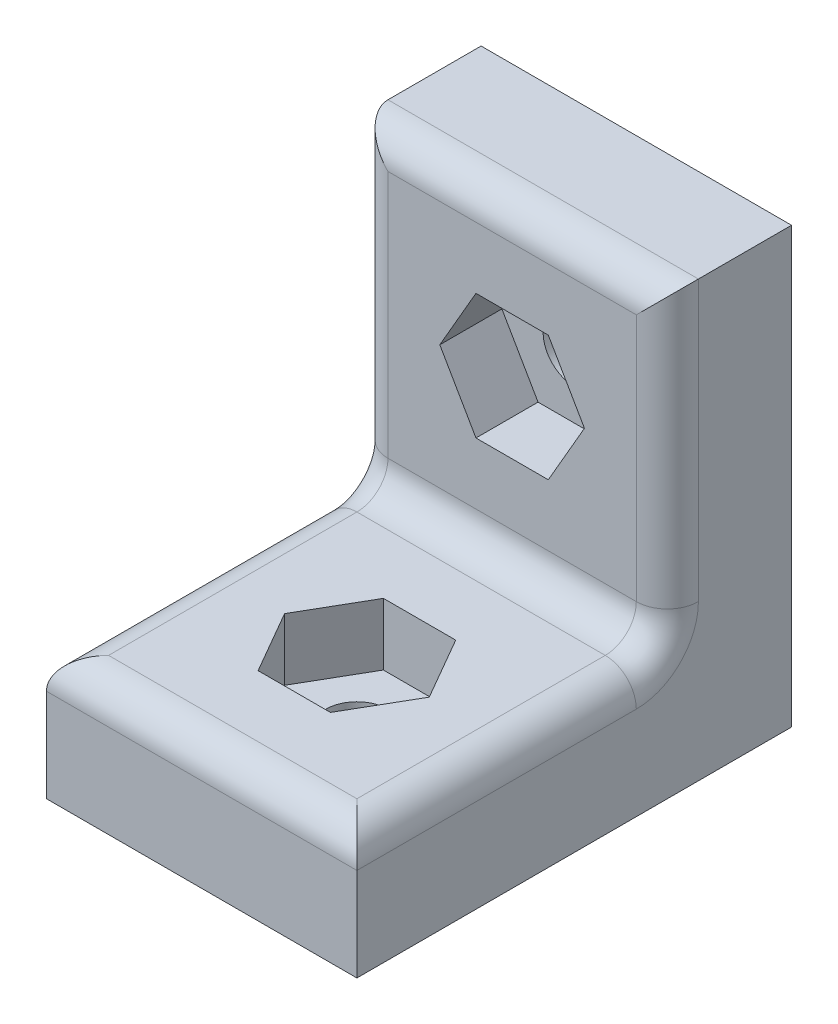
SolidWorks part; units mm, degrees
ref_plane "Plan de face" through (0, 0, 0) normal (0, 0, 1) x (1, 0, 0)
ref_plane "Plan de dessus" through (0, 0, 0) normal (0, 1, 0) x (1, 0, 0)
ref_plane "Plan de droite" through (0, 0, 0) normal (1, 0, 0) x (0, 0, -1)
sketch "Esquisse1" plane through (0, 0, 0) normal (0, 0, 1) x (1, 0, 0)
  line L1 (-5, 14) -> (5, 14)
  line L2 (-5, 14) -> (-5, 0)
  line L3 (-5, 0) -> (5, 0)
  line L4 (5, 14) -> (5, 0)
  dimension "D1" = 10
  dimension "D2" = 14
  dimension "D3" = 5
extrude "Boss.-Extru.1" add sketch "Esquisse1" along normal blind 4
sketch "Esquisse2" plane through (0, 0, 4) normal (0, 0, 1) x (1, 0, 0)
  line L0 (5, 0) -> (5, 14) construction
  line L1 (-5, 0) -> (5, 0)
  line L2 (-5, 0) -> (-5, 4)
  line L3 (-5, 4) -> (5, 4)
  line L4 (5, 0) -> (5, 4)
  dimension "D1" = 4
extrude "Boss.-Extru.2" add sketch "Esquisse2" along normal blind 10
sketch "Esquisse3" plane through (0, 0, 4) normal (0, 0, 1) x (1, 0, 0)
  line L0 (5, 14) -> (-5, 14) construction
  line L1 (-5, 14) -> (-5, 4) construction
  circle A0 centre (0, 9) radius 1
  point P2 (0, 14)
  point P3 (-5, 9)
  dimension "D1" = 2
extrude "Enlèv. mat.-Extru.1" cut sketch "Esquisse3" against normal through all
fillet "Congé1" radius 1 7 edges at (0, 4, 4) (5, 9, 4) (-5, 9, 4) (0, 14, 4) (0, 4, 14) (5, 4, 9) (-5, 4, 9)
sketch "Esquisse4" plane through (0, 4, 0) normal (0, 1, 0) x (1, 0, 0)
  line L0 (5, -14) -> (-5, -14) construction
  line L1 (-5, -14) -> (-5, -4) construction
  circle A0 centre (0, -9) radius 1
  point P0 (0, -14)
  point P1 (-5, -9)
  dimension "D1" = 2
extrude "Enlèv. mat.-Extru.2" cut sketch "Esquisse4" against normal through all
sketch "Esquisse5" plane through (0, 0, 4) normal (0, 0, 1) x (1, 0, 0)
  line L0 (5, 14) -> (-5, 14) construction
  line L1 (1.165, 6.9822) -> (2.33, 9)
  line L2 (2.33, 9) -> (1.165, 11.0178)
  line L3 (1.165, 11.0178) -> (-1.165, 11.0178)
  line L4 (-1.165, 11.0178) -> (-2.33, 9)
  line L5 (-2.33, 9) -> (-1.165, 6.9822)
  line L6 (-1.165, 6.9822) -> (1.165, 6.9822)
  circle A1 centre (0, 9) radius 2.0178 construction
  dimension "D1" = 2.33
extrude "Enlèv. mat.-Extru.3" cut sketch "Esquisse5" against normal blind 2
sketch "Esquisse6" plane through (0, 4, 0) normal (0, 1, 0) x (1, 0, 0)
  line L0 (4, -5) -> (-4, -5) construction
  line L1 (2.33, -9) -> (1.165, -6.9822)
  line L2 (1.165, -6.9822) -> (-1.165, -6.9822)
  line L3 (-1.165, -6.9822) -> (-2.33, -9)
  line L4 (-2.33, -9) -> (-1.165, -11.0178)
  line L5 (-1.165, -11.0178) -> (1.165, -11.0178)
  line L6 (1.165, -11.0178) -> (2.33, -9)
  circle A1 centre (0, -9) radius 2.0178 construction
  dimension "D1" = 2.33
extrude "Enlèv. mat.-Extru.4" cut sketch "Esquisse6" against normal blind 2
